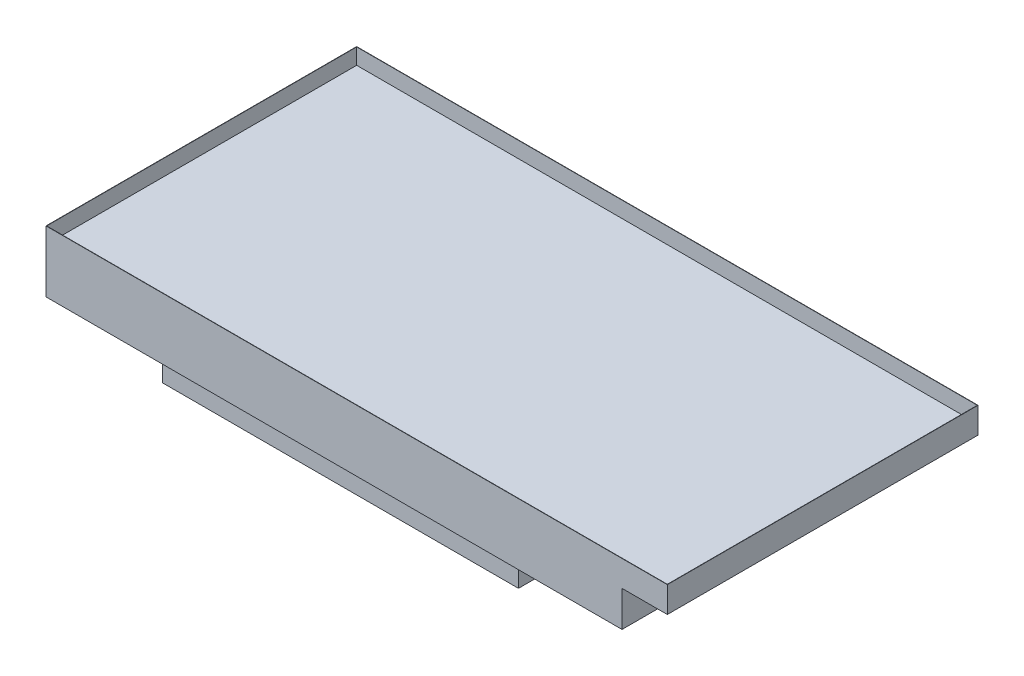
SolidWorks part; units mm, degrees
ref_plane "Front Plane" through (0, 0, 0) normal (0, 0, 1) x (1, 0, 0)
ref_plane "Top Plane" through (0, 0, 0) normal (0, 1, 0) x (1, 0, 0)
ref_plane "Right Plane" through (0, 0, 0) normal (1, 0, 0) x (0, 0, -1)
sketch "Sketch1" plane through (0, 0, 0) normal (0, 0, 1) x (1, 0, 0)
  line L0 (-1376.9163, 1090.1326) -> (3499.8837, 1090.1326)
  line L1 (3499.8837, 1090.1326) -> (3499.8837, 886.9326)
  line L2 (3499.8837, 886.9326) -> (3144.2837, 886.9326)
  line L3 (3144.2837, 886.9326) -> (3144.2837, 607.5326)
  line L4 (3144.2837, 607.5326) -> (2229.8837, 607.5326)
  line L5 (2229.8837, 607.5326) -> (2229.8837, 328.1326)
  line L6 (2229.8837, 328.1326) -> (1874.2837, 328.1326)
  line L7 (1874.2837, 328.1326) -> (1874.2837, 23.3326)
  line L8 (1874.2837, 23.3326) -> (-919.7163, 23.3326)
  line L9 (-1376.9163, 607.5326) -> (-1376.9163, 1090.1326)
  line L10 (-1376.9163, 607.5326) -> (-919.7163, 607.5326)
  line L11 (-919.7163, 607.5326) -> (-919.7163, 23.3326)
  dimension "D2" = 4876.8
  dimension "D3" = 355.6
  dimension "D4" = 914.4
  dimension "D5" = 355.6
  dimension "D6" = 304.8
  dimension "D7" = 279.4
  dimension "D8" = 279.4
  dimension "D9" = 457.2
  dimension "D10" = 584.2
  dimension "D11" = 1066.8
extrude "Boss-Extrude1" add sketch "Sketch1" against normal blind 2438.4
sketch "Sketch4" plane through (-919.7163, 0, 0) normal (-1, 0, 0) x (0, 0, 1)
  line L0 (-2438.4, 23.3326) -> (0, 23.3326) construction
  line L1 (0, 607.5326) -> (-457.2, 607.5326)
  line L2 (0, 607.5326) -> (0, 23.3326)
  line L3 (0, 23.3326) -> (-457.2, 23.3326)
  line L4 (-457.2, 607.5326) -> (-457.2, 23.3326)
  dimension "D1" = 457.2
extrude "Cut-Extrude1" cut sketch "Sketch4" against normal blind 3810
shell "Shell1" thickness 2.54
ref_plane "Plane1" through (0, 963.1326, 0) normal (0, 1, 0) x (1, 0, 0)
sketch "Sketch3" plane through (0, 963.1326, 0) normal (0, 1, 0) x (1, 0, 0)
  line L8 (-1374.3763, 2435.86) -> (3497.3437, 2435.86)
  line L9 (-1374.3763, 2435.86) -> (-1374.3763, 2.54)
  line L10 (-1374.3763, 2.54) -> (3497.3437, 2.54)
  line L11 (3497.3437, 2435.86) -> (3497.3437, 2.54)
extrude "Boss-Extrude3" add sketch "Sketch3" along normal blind 1.778
